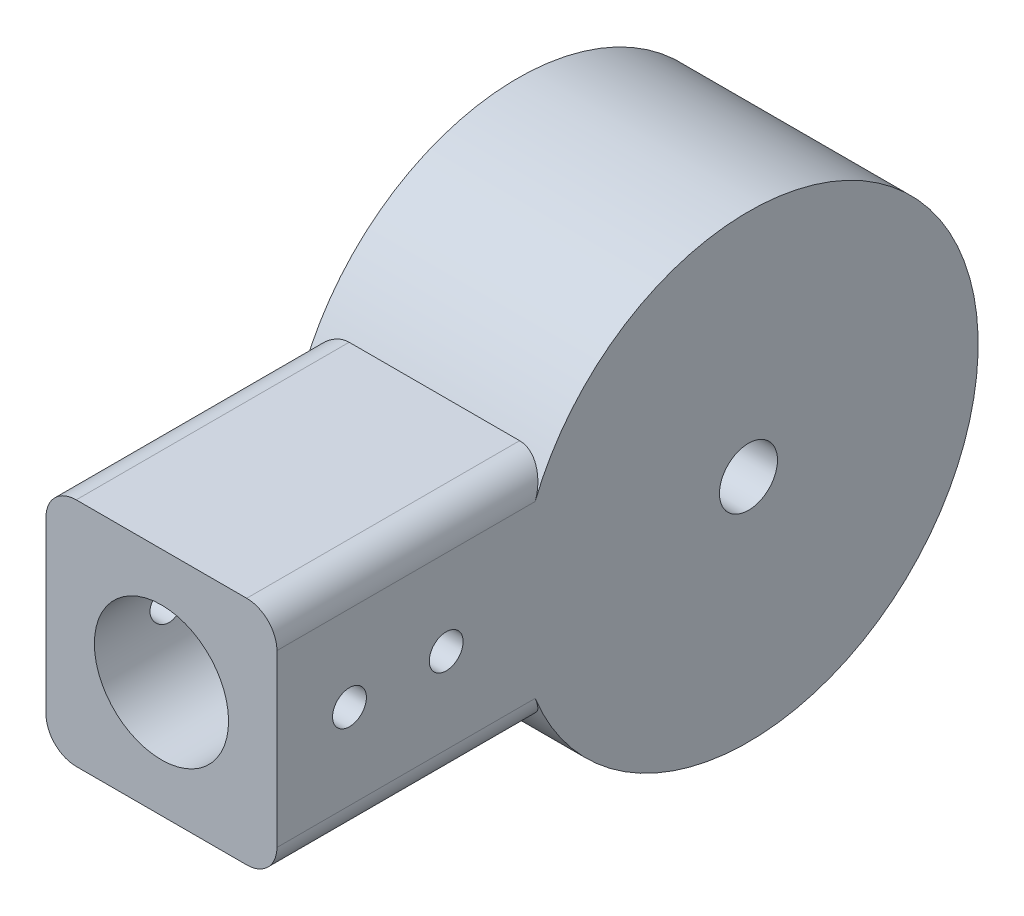
SolidWorks part; units mm, degrees
ref_plane "Front Plane" through (0, 0, 0) normal (0, 0, 1) x (1, 0, 0)
ref_plane "Top Plane" through (0, 0, 0) normal (0, 1, 0) x (1, 0, 0)
ref_plane "Right Plane" through (0, 0, 0) normal (1, 0, 0) x (0, 0, -1)
sketch "Sketch1" plane through (0, 0, 0) normal (0, 1, 0) x (1, 0, 0)
  line L0 (-5.55, -20) -> (-9.55, -20)
  line L1 (-5.55, -20) -> (5.55, -20)
  line L2 (-5.55, -20) -> (-5.55, 0)
  line L3 (-5.55, 0) -> (5.55, 0)
  line L4 (5.55, -20) -> (5.55, 0)
  line L5 (-5.55, -20) -> (5.55, 0) construction
  line L6 (-5.55, 0) -> (5.55, -20) construction
  line L7 (-9.55, -20) -> (-9.55, 0)
  line L8 (-9.55, 4) -> (5.95, 4)
  line L9 (5.95, 4) -> (5.95, 10.55)
  line L10 (5.95, 10.55) -> (-6.05, 10.55)
  line L11 (-6.05, 10.55) -> (-6.05, 27.45)
  line L12 (-6.05, 27.45) -> (5.95, 27.45)
  line L13 (5.95, 27.45) -> (5.95, 34)
  line L14 (5.95, 34) -> (-9.55, 34)
  line L15 (-9.55, 34) -> (-9.55, 38)
  line L16 (-9.55, 38) -> (9.55, 38)
  line L17 (-6.05, 19) -> (-24.2593, 19) construction
  line L18 (9.55, -20) -> (5.55, -20)
  line L19 (-9.55, 0) -> (-9.55, 4)
  line L20 (9.55, 38) -> (9.55, 0)
  line L21 (0, -10) -> (0, 0) construction
  line L22 (9.55, 0) -> (9.55, -20)
  line L23 (-6.05, 19) -> (1.75, 19) construction
  line L24 (-6.05, 21.4) -> (9.55, 21.4)
  line L25 (-6.05, 21.4) -> (-6.05, 16.6)
  line L26 (-6.05, 16.6) -> (9.55, 16.6)
  line L27 (9.55, 21.4) -> (9.55, 16.6)
  line L28 (-6.05, 21.4) -> (9.55, 16.6) construction
  line L29 (-6.05, 16.6) -> (9.55, 21.4) construction
  line L30 (-9.55, 0) -> (-5.55, 0) construction
  line L31 (5.55, 0) -> (9.55, 0) construction
  point P0 (0, -10)
  point P25 (1.75, 19)
  dimension "D1" = 11.1
  dimension "D2" = 4
  dimension "D3" = 20
  dimension "D4" = 30
  dimension "D5" = 16.9
  dimension "D6" = 4.8
  dimension "D7" = 12
  dimension "D8" = 4
  dimension "D9" = 3.5
sketch "Sketch2" plane through (0, 0, 0) normal (0, 1, 0) x (1, 0, 0)
  line L1 (-6.05, 21.4) -> (9.55, 21.4) construction
  line L2 (-6.05, 16.6) -> (9.55, 16.6) construction
  line L3 (9.55, 38) -> (9.55, 0) construction
  line L4 (-9.55, 38) -> (9.55, 38) construction
  line L5 (-9.55, 34) -> (-9.55, 38) construction
  line L6 (5.95, 34) -> (-9.55, 34) construction
  line L7 (5.95, 27.45) -> (5.95, 34) construction
  line L8 (-6.05, 27.45) -> (5.95, 27.45) construction
  line L9 (-6.05, 10.55) -> (-6.05, 27.45) construction
  line L10 (5.95, 10.55) -> (-6.05, 10.55) construction
  line L11 (5.95, 4) -> (5.95, 10.55) construction
  line L12 (-9.55, 4) -> (5.95, 4) construction
  line L13 (-9.55, 0) -> (-9.55, 4) construction
  line L14 (5.55, 0) -> (9.55, 0) construction
  line L15 (-5.55, 0) -> (5.55, 0) construction
  line L16 (-9.55, 0) -> (-5.55, 0) construction
  line L17 (-6.05, 19) -> (-24.2593, 19) construction
  line L18 (-6.05, 21.4) -> (9.55, 21.4)
  line L19 (-6.05, 16.6) -> (9.55, 16.6)
  line L20 (9.55, 38) -> (9.55, 21.4)
  line L21 (-9.55, 38) -> (9.55, 38)
  line L22 (-9.55, 34) -> (-9.55, 38)
  line L23 (5.95, 34) -> (-9.55, 34)
  line L24 (5.95, 27.45) -> (5.95, 34)
  line L25 (-6.05, 27.45) -> (5.95, 27.45)
  line L26 (-6.05, 10.55) -> (-6.05, 16.6)
  line L27 (5.95, 10.55) -> (-6.05, 10.55)
  line L28 (5.95, 4) -> (5.95, 10.55)
  line L29 (-9.55, 4) -> (5.95, 4)
  line L30 (-9.55, 0) -> (-9.55, 4)
  line L31 (5.55, 0) -> (9.55, 0)
  line L32 (-5.55, 0) -> (5.55, 0)
  line L33 (-9.55, 0) -> (-5.55, 0)
  line L34 (-6.05, 21.4) -> (-6.05, 27.45)
  line L35 (9.55, 16.6) -> (9.55, 0)
  line L36 (-6.05, 19) -> (1.75, 19) construction
  line L37 (-6.05, 19) -> (-24.2593, 19) construction
  line L38 (-6.05, 19) -> (1.75, 19) construction
revolve "Revolve1" add sketch "Sketch2" angle 360 about L37
sketch "Sketch3" plane through (0, 0, 0) normal (0, 0, 1) x (1, 0, 0)
  line L0 (-9.55, 0) -> (9.55, 0) construction
  line L1 (-5.55, 0) -> (5.55, 0) construction
  line L2 (-5.55, 0) -> (5.55, 0)
  line L3 (-9.55, 19) -> (-9.55, -19) construction
  line L4 (9.55, 9.55) -> (-9.55, 9.55)
  line L5 (9.55, 9.55) -> (9.55, -9.55)
  line L6 (9.55, -9.55) -> (-9.55, -9.55)
  line L7 (-9.55, 9.55) -> (-9.55, -9.55)
  line L8 (9.55, 9.55) -> (-9.55, -9.55) construction
  line L9 (9.55, -9.55) -> (-9.55, 9.55) construction
  circle A0 centre (0, 0) radius 5.55
  point P4 (9.55, 0)
  point P5 (-9.55, 0)
extrude "Boss-Extrude1" add sketch "Sketch3" along normal up to vertex and the other way up to surface contours L4 L7 L6 L5 A0
fillet "Fillet1" radius 2.5 4 edges at (-9.55, 9.55, 8.7128) (-9.55, -9.55, 8.7128) (9.55, 9.55, 8.7128) (9.55, -9.55, 8.7128)
sketch "Sketch4" plane through (0, 0, 0) normal (1, 0, 0) x (0, 0, -1)
  line L0 (-6, 0) -> (0, 0) construction
  line L1 (-6, 0) -> (-14, 0) construction
  line L3 (-14, 0) -> (-20, 0) construction
  line L4 (-20, 7.05) -> (-20, -7.05) construction
  circle A0 centre (-6, 0) radius 1.4
  circle A1 centre (-14, 0) radius 1.4
  dimension "D1" = 2.8
  dimension "D2" = 8
extrude "Cut-Extrude1" cut sketch "Sketch4" against normal through all both and the other way through all
